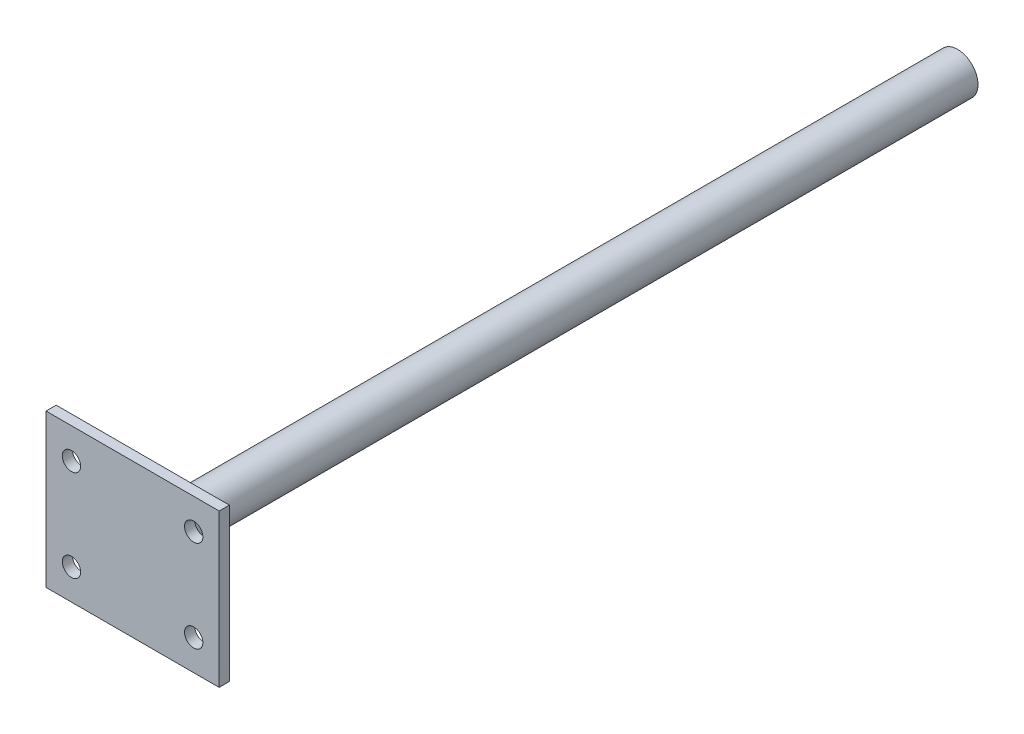
SolidWorks part; units mm, degrees
ref_plane "Front Plane" through (0, 0, 0) normal (0, 0, 1) x (1, 0, 0)
ref_plane "Top Plane" through (0, 0, 0) normal (0, 1, 0) x (1, 0, 0)
ref_plane "Right Plane" through (0, 0, 0) normal (1, 0, 0) x (0, 0, -1)
sketch "Sketch1" plane through (0, 0, 0) normal (0, 0, 1) x (1, 0, 0)
  line L0 (0, 22.04) -> (0, -20.4282) construction
  line L1 (-17, 15) -> (17, 15)
  line L2 (-17, 15) -> (-17, -15)
  line L3 (-17, -15) -> (17, -15)
  line L4 (17, 15) -> (17, -15)
  line L5 (-17, 15) -> (17, -15) construction
  line L6 (-17, -15) -> (17, 15) construction
  line L7 (-31.0989, 0) -> (30.1968, 0) construction
  circle A0 centre (-12, 9) radius 1.8
  circle A1 centre (12, 9) radius 1.8
  circle A2 centre (12, -9) radius 1.8
  circle A3 centre (-12, -9) radius 1.8
  point P0 (0, 0)
  dimension "D5" = 3.6
  dimension "D1" = 34
  dimension "D2" = 30
  dimension "D3" = 12
  dimension "D4" = 24
extrude "Boss-Extrude1" add sketch "Sketch1" along normal blind 2
scale "Scale1" scale about centroid uniform scaling yes scale factor 1.25
sketch "Sketch2" plane through (0, 0, -0.25) normal (0, 0, -1) x (-1, 0, 0)
  circle A0 centre (0, 0) radius 5
extrude "Boss-Extrude3" add sketch "Sketch2" along normal blind 200
fillet "Fillet2" radius 2 1 edges at (-5, 0, -0.25)
